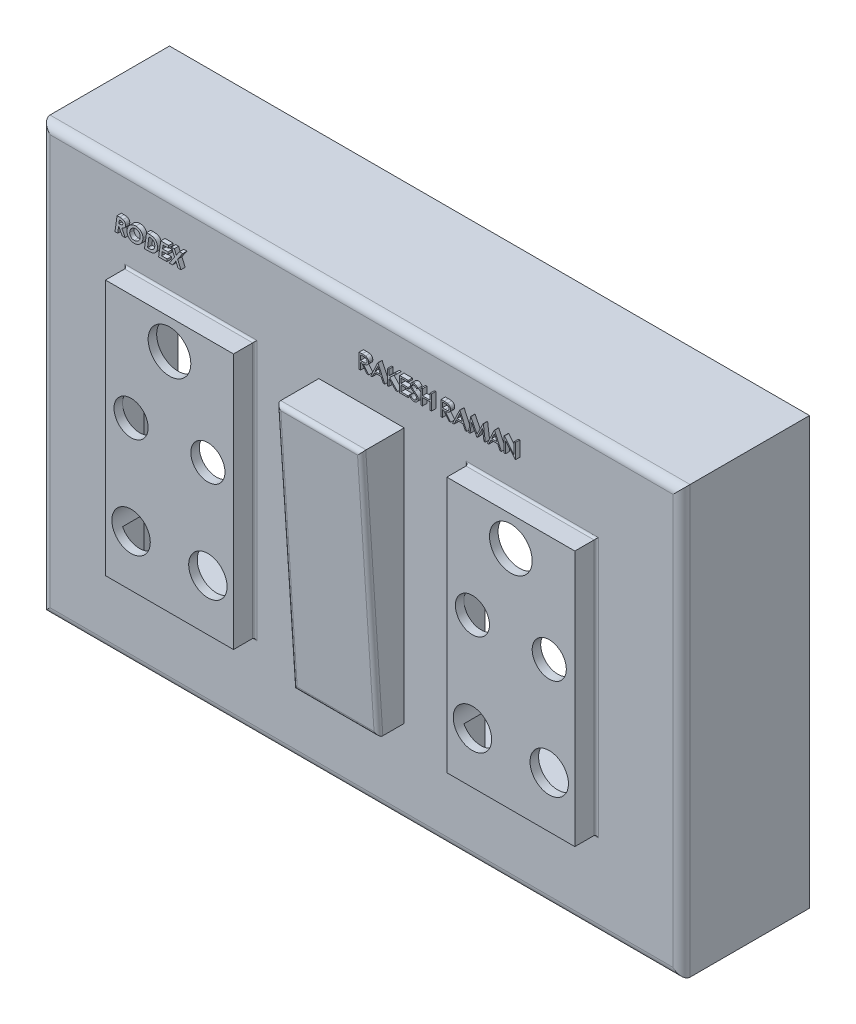
SolidWorks part; units mm, degrees
ref_plane "Front Plane" through (0, 0, 0) normal (0, 0, 1) x (1, 0, 0)
ref_plane "Top Plane" through (0, 0, 0) normal (0, 1, 0) x (1, 0, 0)
ref_plane "Right Plane" through (0, 0, 0) normal (1, 0, 0) x (0, 0, -1)
sketch "Sketch1" plane through (0, 0, 0) normal (0, 0, 1) x (1, 0, 0)
  line L1 (-75, 50) -> (75, 50)
  line L2 (-75, 50) -> (-75, -50)
  line L3 (-75, -50) -> (75, -50)
  line L4 (75, 50) -> (75, -50)
  line L5 (-75, 50) -> (75, -50) construction
  line L6 (-75, -50) -> (75, 50) construction
  point P0 (0, 0)
  dimension "D1" = 150
  dimension "D2" = 100
extrude "Boss-Extrude1" add sketch "Sketch1" along normal blind 30
sketch "Sketch2" plane through (0, 0, 30) normal (0, 0, 1) x (1, 0, 0)
  line L1 (-55, 30) -> (-25, 30)
  line L2 (-55, 30) -> (-55, -30)
  line L3 (-55, -30) -> (-25, -30)
  line L4 (-25, 30) -> (-25, -30)
  line L5 (-55, 30) -> (-25, -30) construction
  line L6 (-55, -30) -> (-25, 30) construction
  point P0 (-40, 0)
  dimension "D1" = 30
  dimension "D2" = 60
  dimension "D3" = 40
extrude "Boss-Extrude2" add sketch "Sketch2" along normal blind 5
pattern_linear "LPattern1" count 2 spacing 80 along (1, 0, 0) of "Boss-Extrude2"
shell "Shell2" thickness 2
sketch "Sketch3" plane through (0, 0, 35) normal (0, 0, 1) x (1, 0, 0)
  line L0 (-55, 30) -> (-55, -30) construction
  line L1 (-55, -30) -> (-25, -30) construction
  line L2 (-25, 30) -> (-55, 30) construction
  line L3 (-25, 30) -> (-55, 30) construction
  line L4 (55, 30) -> (25, 30) construction
  line L5 (25, 30) -> (25, -30) construction
  circle A0 centre (-40, 23) radius 5
  circle A1 centre (-49, 5) radius 4
  circle A2 centre (-31, 5) radius 4
  circle A3 centre (-49, -18) radius 4.5
  circle A4 centre (-31, -18) radius 4.5
  circle A5 centre (31, 5) radius 4
  circle A6 centre (40, 23) radius 5
  circle A7 centre (49, 5) radius 4
  circle A8 centre (31, -18) radius 4.5
  circle A9 centre (49, -18) radius 4.5
  point P24 (-40, 30)
  dimension "D1" = 9
  dimension "D2" = 8
  dimension "D3" = 10
  dimension "D4" = 6
  dimension "D5" = 18
  dimension "D6" = 12
  dimension "D7" = 6
  dimension "D8" = 7
  dimension "D9" = 25
  dimension "D11" = 7
  dimension "D12" = 6
  dimension "D10" = 2
extrude "Cut-Extrude1" cut sketch "Sketch3" against normal blind 36
sketch "Sketch8" plane through (0, 0, 0) normal (1, 0, 0) x (0, 0, -1)
  line L0 (-30, 30) -> (-40, 30)
  line L1 (-40, 30) -> (-36, -30)
  line L2 (-36, -30) -> (-30, -30)
  line L3 (-30, -30) -> (-30, 30)
  dimension "D1" = 10
  dimension "D2" = 6
extrude "Boss-Extrude3" add sketch "Sketch8" along normal mid plane 20
fillet "Fillet1" radius 2 4 edges at (75, 0, 30) (0, -50, 30) (0, 50, 30) (-75, 0, 30)
fillet "Fillet2" radius 0.5 8 edges at (40, 30, 30) (25, 0, 30) (40, -30, 30) (55, 0, 30) (-40, -30, 30) (-25, 0, 30) (-40, 30, 30) (-55, 0, 30)
fillet "Fillet3" radius 1 4 edges at (0, 30, 40) (10, 0, 38) (0, -30, 36) (-10, 0, 38)
sketch "Sketch9" plane through (0, 0, 30) normal (0, 0, 1) x (1, 0, 0)
  line L0 (-26.9806, 36.9224) -> (-71.6729, 36.9224) construction
  text T0 "<b><i>RODEX</i></b>"
extrude "Boss-Extrude4" add sketch "Sketch9" along normal blind 1
sketch "Sketch10" plane through (0, 0, 30) normal (0, 0, 1) x (1, 0, 0)
  line L0 (0, 37.5935) -> (61.2397, 37.5935) construction
  text T0 "RAKESH RAMAN"
extrude "Boss-Extrude5" add sketch "Sketch10" along normal blind 1
